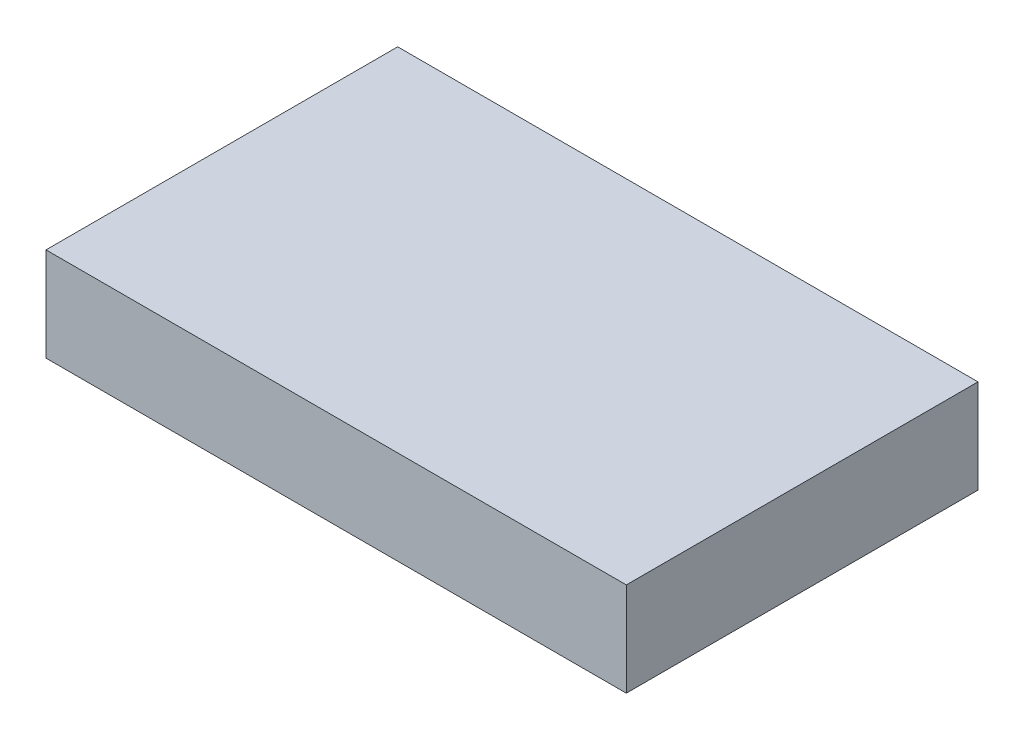
SolidWorks part; units mm, degrees
ref_plane "Front Plane" through (0, 0, 0) normal (0, 0, 1) x (1, 0, 0)
ref_plane "Top Plane" through (0, 0, 0) normal (0, 1, 0) x (1, 0, 0)
ref_plane "Right Plane" through (0, 0, 0) normal (1, 0, 0) x (0, 0, -1)
sketch "Sketch1" plane through (0, 0, 0) normal (0, 1, 0) x (1, 0, 0)
  line L1 (0, 0) -> (9.9, 0)
  line L2 (0, 0) -> (0, 6)
  line L3 (0, 6) -> (9.9, 6)
  line L4 (9.9, 0) -> (9.9, 6)
  dimension "D1" = 6
  dimension "D2" = 9.9
extrude "Boss-Extrude1" add sketch "Sketch1" along normal blind 1.6
